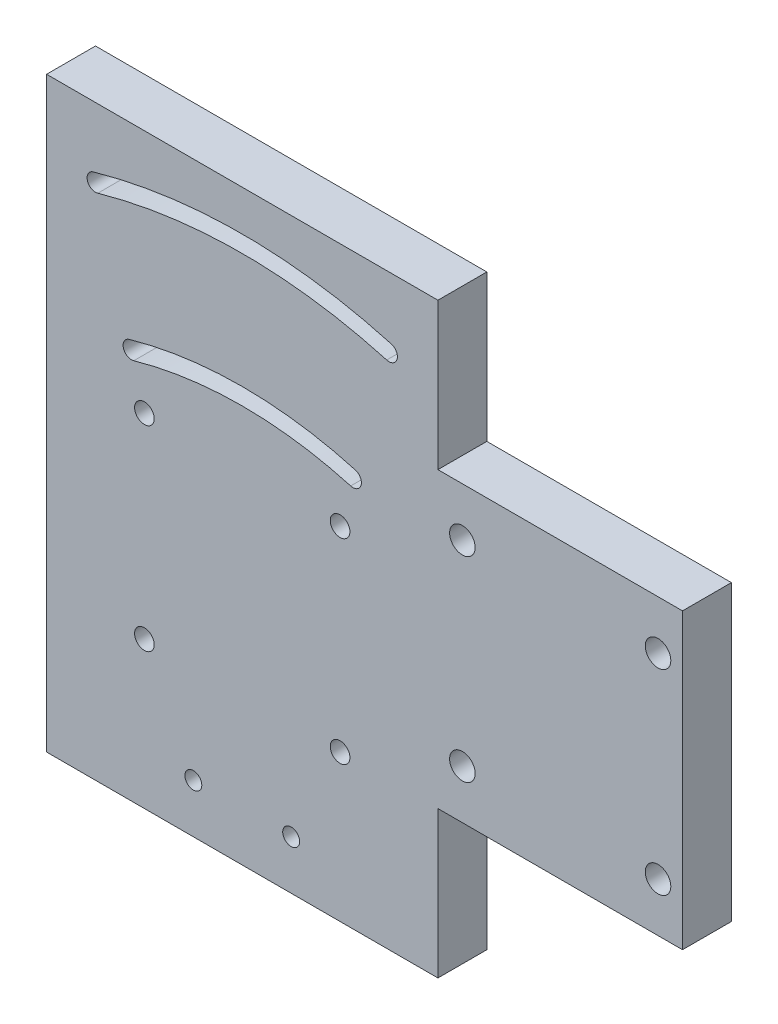
SolidWorks part; units mm, degrees
ref_plane "Front" through (0, 0, 0) normal (0, 0, 1) x (1, 0, 0)
ref_plane "Top" through (0, 0, 0) normal (0, 1, 0) x (1, 0, 0)
ref_plane "Right" through (0, 0, 0) normal (1, 0, 0) x (0, 0, -1)
sketch "Sketch1" plane through (0, 0, 0) normal (0, 0, 1) x (1, 0, 0)
  line L1 (0, 0) -> (101.6, 0)
  line L2 (0, 0) -> (0, 152.4)
  line L3 (0, 152.4) -> (101.6, 152.4)
  line L4 (101.6, 0) -> (101.6, 152.4)
  line L5 (101.6, 114.3) -> (165.1, 114.3)
  line L6 (101.6, 152.4) -> (101.6, 114.3)
  line L7 (101.6, 114.3) -> (101.6, 38.1)
  line L8 (101.6, 38.1) -> (165.1, 38.1)
  line L9 (165.1, 114.3) -> (165.1, 38.1)
  dimension "D1" = 152.4
  dimension "D2" = 101.6
  dimension "D3" = 76.2
  dimension "D4" = 63.5
  dimension "D5" = 38.1
extrude "Extrude1" add sketch "Sketch1" along normal blind 12.7
sketch "Sketch4" plane through (0, 0, 12.7) normal (0, 0, 1) x (1, 0, 0)
  line L0 (101.6, 114.3) -> (165.1, 114.3) construction
  line L1 (165.1, 114.3) -> (165.1, 38.1) construction
  line L2 (0, 0) -> (101.6, 0) construction
  line L3 (101.6, 0) -> (101.6, 152.4) construction
  circle A0 centre (158.75, 101.6) radius 3.3147
  circle A1 centre (76.2, 88.9) radius 2.5527
  dimension "D3" = 6.6294
  dimension "D6" = 5.1054
  dimension "D1" = 12.7
  dimension "D2" = 6.35
  dimension "D4" = 88.9
  dimension "D5" = 25.4
extrude "Cut-Extrude2" cut sketch "Sketch4" against normal blind 12.7
pattern_linear "LPattern2" count 2 spacing 50.8 count 2 spacing 50.8
sketch "Sketch5" plane through (0, 0, 12.7) normal (0, 0, 1) x (1, 0, 0)
  line L1 (0, 0) -> (0, 152.4) construction
  line L2 (50.8, 0) -> (12.7, 134.4042) construction
  line L3 (50.8, 0) -> (88.9, 134.4042) construction
  line L4 (0, 0) -> (101.6, 0) construction
  line L5 (101.6, 0) -> (101.6, 152.4) construction
  arc A0 (12.7, 134.4042) -> (88.9, 134.4042) centre (50.8, 0) cw construction
  arc A1 (22.0518, 101.4141) -> (79.5482, 101.4141) centre (50.8, 0) cw construction
  arc A2 (22.6476, 99.3125) -> (78.9524, 99.3125) centre (50.8, 0) cw
  arc A3 (21.4561, 103.5156) -> (80.1439, 103.5156) centre (50.8, 0) cw
  arc A4 (13.2957, 132.3026) -> (88.3043, 132.3026) centre (50.8, 0) cw
  arc A5 (12.1043, 136.5058) -> (89.4957, 136.5058) centre (50.8, 0) cw
  arc A6 (88.3043, 132.3026) -> (89.4957, 136.5058) centre (88.9, 134.4042) ccw
  arc A7 (12.1043, 136.5058) -> (13.2957, 132.3026) centre (12.7, 134.4042) ccw
  arc A8 (21.4561, 103.5156) -> (22.6476, 99.3125) centre (22.0518, 101.4141) ccw
  circle A9 centre (38.1, 12.7) radius 2.1971
  arc A10 (78.9524, 99.3125) -> (80.1439, 103.5156) centre (79.5482, 101.4141) ccw
  circle A11 centre (63.5, 12.7) radius 2.1971
  point P0 (50.8, 0)
  dimension "D6" = 105.41
  dimension "D13" = 4.3942
  dimension "D16" = 4.3942
  dimension "D2" = 50.8
  dimension "D3" = 12.7
  dimension "D4" = 139.7
  dimension "D5" = 12.7
  dimension "D11" = 12.7
  dimension "D12" = 12.7
  dimension "D14" = 12.7
  dimension "D15" = 12.7
  dimension "D7" = 2.1844
  dimension "D8" = 2.1844
  dimension "D9" = 2.1844
  dimension "D10" = 2.1844
extrude "Cut-Extrude4" cut sketch "Sketch5" against normal through all
